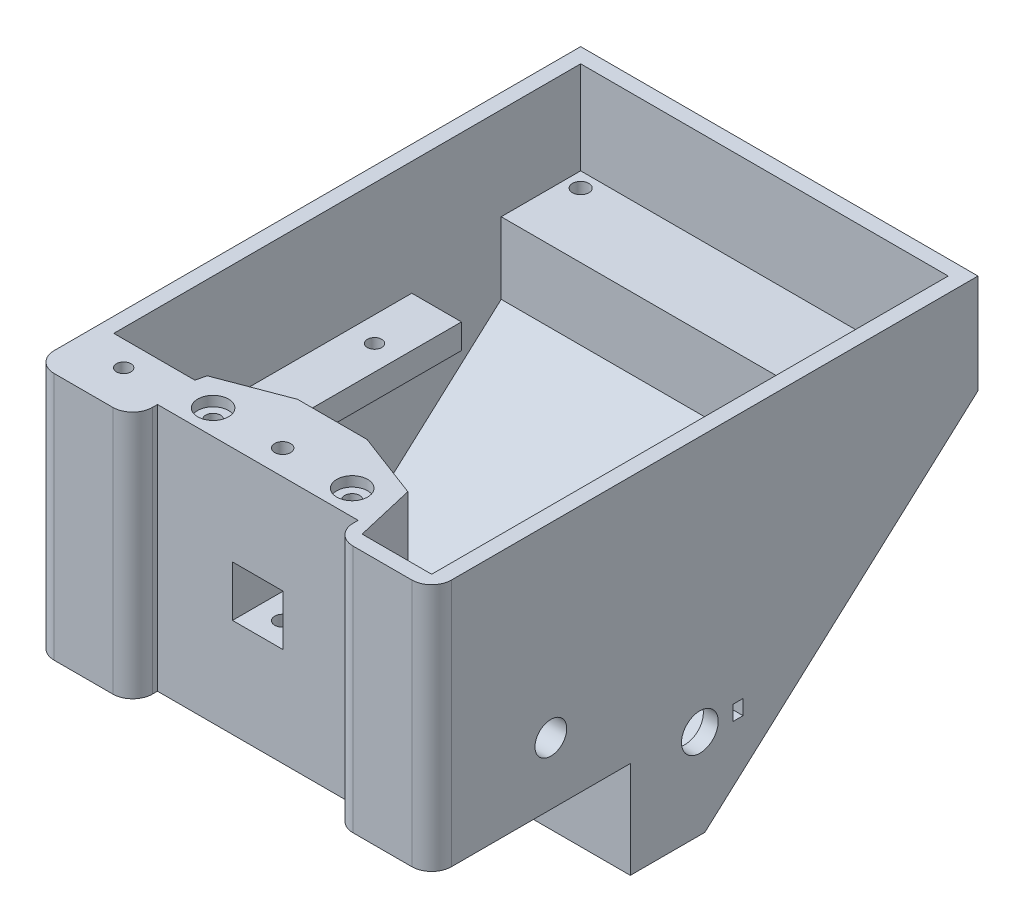
SolidWorks part; units mm, degrees
ref_plane "Спереди" through (0, 0, 0) normal (0, 0, 1) x (1, 0, 0)
ref_plane "Сверху" through (0, 0, 0) normal (0, 1, 0) x (1, 0, 0)
ref_plane "Справа" through (0, 0, 0) normal (1, 0, 0) x (0, 0, -1)
sketch "Sketch2" plane through (0, 0, 0) normal (1, 0, 0) x (0, 0, -1)
  line L0 (-27.3205, 20.9982) -> (-27.3205, -29.0018)
  line L1 (-27.3205, -29.0018) -> (12.6795, -29.0018)
  line L2 (12.6795, -29.0018) -> (12.6795, -48.5114)
  line L3 (12.6795, -48.5114) -> (27.6795, -48.5114)
  line L4 (82.6795, 20.9982) -> (82.6795, 0.9982)
  line L5 (82.6795, 20.9982) -> (-27.3205, 20.9982)
  line L6 (82.6795, 0.9982) -> (27.6795, -48.5114)
  dimension "D1" = 110
  dimension "D2" = 50
  dimension "D3" = 40
  dimension "D4" = 15
  dimension "D5" = 20
extrude "Boss-Extrude1" add sketch "Sketch2" along normal blind 80
shell "Shell1" thickness 3
sketch "Sketch3" plane through (0, 0, 24.3205) normal (0, 0, -1) x (-1, 0, 0)
  line L0 (-40, 20.9982) -> (-40, -26.0018) construction
  line L3 (-77, 20.9982) -> (-3, 20.9982) construction
  line L4 (-77, -26.0018) -> (-3, -26.0018) construction
  line L6 (-17, 20.9982) -> (-63, 20.9982)
  line L7 (-17, 20.9982) -> (-17, -26.0018)
  line L8 (-17, -26.0018) -> (-63, -26.0018)
  line L9 (-63, 20.9982) -> (-63, -26.0018)
  line L10 (-17, 20.9982) -> (-63, -26.0018) construction
  line L11 (-17, -26.0018) -> (-63, 20.9982) construction
  point P6 (-40, -2.5018)
  dimension "D1" = 46
extrude "Boss-Extrude2" add sketch "Sketch3" along normal blind 17
sketch "Sketch4" plane through (0, 0, 27.3205) normal (0, 0, 1) x (1, 0, 0)
  line L0 (0, 20.9982) -> (80, -29.0018) construction
  line L2 (45.1, -9.1018) -> (34.9, -9.1018)
  line L3 (45.1, -9.1018) -> (45.1, 1.0982)
  line L4 (45.1, 1.0982) -> (34.9, 1.0982)
  line L5 (34.9, -9.1018) -> (34.9, 1.0982)
  line L6 (45.1, -9.1018) -> (34.9, 1.0982) construction
  line L7 (45.1, 1.0982) -> (34.9, -9.1018) construction
  point P4 (40, -4.0018)
  dimension "D1" = 10.2
extrude "Cut-Extrude1" cut sketch "Sketch4" against normal up to surface (20 mm away) up to face at (40, -2.5018, 7.3205)
sketch "Sketch6" plane through (0, -29.0018, 0) normal (0, -1, 0) x (1, 0, 0)
  line L0 (40, 27.3205) -> (40, -12.6795) construction
  line L1 (47.5, -5.4795) -> (32.5, -5.4795) construction
  line L2 (47.5, -5.4795) -> (47.5, 7.3205) construction
  line L3 (47.5, 7.3205) -> (32.5, 7.3205) construction
  line L4 (32.5, -5.4795) -> (32.5, 7.3205) construction
  line L5 (47.5, -5.4795) -> (32.5, 7.3205) construction
  line L6 (47.5, 7.3205) -> (32.5, -5.4795) construction
  line L7 (80, -12.6795) -> (0, -12.6795) construction
  line L8 (51.5, 0.9205) -> (28.5, 0.9205) construction
  line L9 (80, 27.3205) -> (0, 27.3205) construction
  line L11 (44, 7.3205) -> (59, 7.3205)
  line L12 (44, 7.3205) -> (44, -5.4795)
  line L13 (44, -5.4795) -> (59, -5.4795)
  line L14 (59, 7.3205) -> (59, -5.4795)
  line L15 (44, 7.3205) -> (59, -5.4795) construction
  line L16 (44, -5.4795) -> (59, 7.3205) construction
  line L17 (36, 7.3205) -> (21, 7.3205)
  line L18 (36, 7.3205) -> (36, -5.4795)
  line L19 (36, -5.4795) -> (21, -5.4795)
  line L20 (21, 7.3205) -> (21, -5.4795)
  line L21 (36, 7.3205) -> (21, -5.4795) construction
  line L22 (36, -5.4795) -> (21, 7.3205) construction
  point P0 (40, 0.9205)
  point P14 (40, 0.9205)
  dimension "D1" = 15
  dimension "D2" = 12.8
  dimension "D3" = 8
  dimension "D4" = 20
extrude "Cut-Extrude2" cut sketch "Sketch6" against normal up to surface (3 mm away) up to face at (40, -26.0018, 10.0705)
sketch "Sketch7" plane through (0, 0, 27.3205) normal (0, 0, 1) x (1, 0, 0)
  line L0 (40, 20.9982) -> (40, -29.0018) construction
  line L1 (80, 20.9982) -> (0, 20.9982) construction
  line L2 (80, -29.0018) -> (0, -29.0018) construction
  line L4 (60.2, -29.0018) -> (19.8, -29.0018)
  line L5 (60.2, -29.0018) -> (60.2, 20.9982)
  line L6 (60.2, 20.9982) -> (19.8, 20.9982)
  line L7 (19.8, -29.0018) -> (19.8, 20.9982)
  line L8 (60.2, -29.0018) -> (19.8, 20.9982) construction
  line L9 (60.2, 20.9982) -> (19.8, -29.0018) construction
  point P6 (40, -4.0018)
  dimension "D1" = 40.4
extrude "Cut-Extrude3" cut sketch "Sketch7" against normal blind 5
fillet "Fillet1" radius 4 4 edges at (19.8, -4.0018, 27.3205) (60.2, -4.0018, 27.3205) (80, -4.0018, 27.3205) (0, -4.0018, 27.3205)
sketch "Sketch12" plane through (0, 20.9982, 0) normal (0, 1, 0) x (1, 0, 0)
  line L0 (19.8, -22.3205) -> (19.8, -12.3205) construction
  line L1 (19.8, -12.3205) -> (60.2, -12.3205) construction
  line L2 (60.2, -12.3205) -> (60.2, -22.3205) construction
  line L3 (33, -7.3205) -> (19.8, -12.3205)
  line L4 (17, -7.3205) -> (63, -7.3205) construction
  line L5 (19.8, -12.3205) -> (17, -24.3205)
  line L6 (17, -24.3205) -> (17, -7.3205)
  line L7 (17, -7.3205) -> (33, -7.3205)
  line L8 (47, -7.3205) -> (63, -7.3205)
  line L9 (63, -7.3205) -> (63, -24.3205)
  line L10 (63, -24.3205) -> (60.2, -12.3205)
  line L11 (60.2, -12.3205) -> (47, -7.3205)
  dimension "D1" = 10
  dimension "D2" = 16
extrude "Cut-Extrude7" cut sketch "Sketch12" against normal up to surface (47 mm away) up to face at (40, -26.0018, 5.4955)
sketch "Sketch13" plane through (0, 20.9982, 0) normal (0, 1, 0) x (1, 0, 0)
  line L0 (19.8, -22.3205) -> (19.8, -12.3205) construction
  line L1 (19.8, -12.3205) -> (60.2, -12.3205) construction
  line L2 (60.2, -12.3205) -> (60.2, -22.3205) construction
  line L3 (60.2, -17.3205) -> (19.8, -17.3205) construction
  circle A0 centre (26, -17.3205) radius 1.5
  circle A1 centre (54, -17.3205) radius 1.5
  point P14 (40, -17.3205)
  dimension "D1" = 3
  dimension "D2" = 28
  dimension "D3" = 14
  dimension "D4" = 6.2
extrude "Cut-Extrude8" cut sketch "Sketch13" against normal blind 25
sketch "Sketch14" plane through (0, 20.9982, 0) normal (0, 1, 0) x (1, 0, 0)
  circle A0 centre (26, -17.3205) radius 3.1
  circle A1 centre (54, -17.3205) radius 3.1
  dimension "D1" = 6.2
extrude "Cut-Extrude9" cut sketch "Sketch14" against normal blind 2
sketch "Sketch17" plane through (77, 0, 0) normal (-1, 0, 0) x (0, 0, 1)
  line L0 (-45.6795, -2.0018) -> (-0.6795, -2.0018)
  line L1 (-0.6795, -2.0018) -> (-0.6795, -7.0018)
  line L2 (-0.6795, -7.0018) -> (-45.6795, -7.0018)
  line L3 (-45.6795, -7.0018) -> (-45.6795, -2.0018)
  line L4 (-79.6795, 20.9982) -> (24.3205, 20.9982) construction
  line L5 (-79.6795, 2.3342) -> (-79.6795, 20.9982) construction
  dimension "D1" = 45
  dimension "D2" = 5
  dimension "D3" = 23
  dimension "D4" = 34
extrude "Boss-Extrude5" add sketch "Sketch17" along normal up to surface (74 mm away) up to face at (3, -14.0994, -24.0865)
sketch "Sketch18" plane through (0, -2.0018, 0) normal (0, 1, 0) x (1, 0, 0)
  line L0 (40, 0.6795) -> (40, 45.6795) construction
  line L1 (3, 0.6795) -> (77, 0.6795) construction
  line L2 (3, 45.6795) -> (77, 45.6795) construction
  line L3 (77, 0.6795) -> (77, 45.6795) construction
  line L4 (13, 0.6795) -> (67, 0.6795)
  line L5 (13, 0.6795) -> (13, 45.6795)
  line L6 (13, 45.6795) -> (67, 45.6795)
  line L7 (67, 0.6795) -> (67, 45.6795)
  line L8 (13, 0.6795) -> (67, 45.6795) construction
  line L9 (13, 45.6795) -> (67, 0.6795) construction
  point P6 (40, 23.1795)
  dimension "D1" = 10
extrude "Cut-Extrude10" cut sketch "Sketch18" against normal up to next
sketch "Sketch19" plane through (0, -2.0018, 0) normal (0, 1, 0) x (1, 0, 0)
  line L0 (72, 45.6795) -> (72, 0.6795) construction
  line L1 (67, 45.6795) -> (77, 45.6795) construction
  line L2 (67, 0.6795) -> (77, 0.6795) construction
  line L3 (8, 45.6795) -> (8, 0.6795) construction
  line L4 (3, 45.6795) -> (13, 45.6795) construction
  line L5 (3, 0.6795) -> (13, 0.6795) construction
  circle A0 centre (72, 37.1795) radius 1.45
  circle A1 centre (72, 6.1795) radius 1.45
  circle A2 centre (8, 33.1795) radius 1.45
  circle A3 centre (8, 6.1795) radius 1.45
  point P20 (72, 23.1795)
  point P21 (8, 23.1795)
  dimension "D1" = 2.9
  dimension "D2" = 14
  dimension "D3" = 17
  dimension "D4" = 17
  dimension "D5" = 10
extrude "Cut-Extrude11" cut sketch "Sketch19" against normal up to next
sketch "Sketch21" plane through (0, -26.0018, 0) normal (0, 1, 0) x (1, 0, 0)
  line L0 (3, -24.3205) -> (3, -14.3205)
  line L1 (3, -24.3205) -> (3, 15.6795) construction
  line L2 (3, -14.3205) -> (19.3333, -14.3205)
  line L3 (19.8, -12.3205) -> (17, -24.3205) construction
  line L4 (19.3333, -14.3205) -> (17, -24.3205)
  line L6 (3, -24.3205) -> (17, -24.3205)
  dimension "D1" = 10
extrude "Boss-Extrude6" add sketch "Sketch21" along normal up to surface (47 mm away) up to face at (54, 20.9982, 20.4205)
sketch "Sketch22" plane through (0, 20.9982, 0) normal (0, 1, 0) x (1, 0, 0)
  line L0 (0, 82.6795) -> (0, -23.3205) construction
  line L1 (15.8, -27.3205) -> (4, -27.3205) construction
  circle A0 centre (10, -19.3205) radius 1.45
  dimension "D1" = 2.9
  dimension "D2" = 10
  dimension "D3" = 8
extrude "Cut-Extrude12" cut sketch "Sketch22" against normal through all
sketch "Sketch24" plane through (80, 0, 0) normal (1, 0, 0) x (0, 0, -1)
  line L0 (12.6795, -48.5114) -> (27.6795, -48.5114) construction
  line L1 (12.6795, -29.0018) -> (12.6795, -48.5114) construction
  line L2 (18.1795, -30.5114) -> (18.1795, -19.0114) construction
  line L3 (18.1795, -19.0114) -> (35.1795, -19.0114) construction
  line L4 (35.1795, -19.0114) -> (35.1795, -30.5114) construction
  line L5 (26.6795, -19.0114) -> (26.6795, -39.0114) construction
  line L6 (30.3795, -30.5114) -> (34.3795, -30.5114) construction
  line L8 (33.3795, -32.0114) -> (35.3795, -32.0114)
  line L9 (33.3795, -32.0114) -> (33.3795, -29.0114)
  line L10 (33.3795, -29.0114) -> (35.3795, -29.0114)
  line L11 (35.3795, -32.0114) -> (35.3795, -29.0114)
  line L12 (33.3795, -32.0114) -> (35.3795, -29.0114) construction
  line L13 (33.3795, -29.0114) -> (35.3795, -32.0114) construction
  circle A0 centre (26.6795, -30.5114) radius 3.7
  circle A1 centre (26.6795, -30.5114) radius 8.5 construction
  dimension "D1" = 7.4
  dimension "D2" = 17
  dimension "D3" = 18
  dimension "D4" = 14
  dimension "D5" = 20
  dimension "D6" = 4
  dimension "D7" = 2
  dimension "D8" = 3
extrude "Cut-Extrude13" cut sketch "Sketch24" against normal up to next
sketch "Sketch26" plane through (3, 0, 0) normal (1, 0, 0) x (0, 0, -1)
  line L0 (79.6795, 2.3342) -> (63.6795, 2.3342)
  line L1 (63.6795, 2.3342) -> (63.6795, -12.0686)
  line L2 (26.5281, -45.5114) -> (79.6795, 2.3342) construction
  line L3 (63.6795, -12.0686) -> (79.6795, 2.3342)
  dimension "D1" = 16
extrude "Boss-Extrude7" add sketch "Sketch26" along normal up to surface (74 mm away) up to face at (77, -30.5114, -34.3795)
sketch "Sketch27" plane through (0, 2.3342, 0) normal (0, 1, 0) x (1, 0, 0)
  line L0 (3, 76.6795) -> (77, 76.6795) construction
  line L1 (3, 79.6795) -> (3, 63.6795) construction
  line L2 (77, 79.6795) -> (77, 63.6795) construction
  line L3 (80, 82.6795) -> (0, 82.6795) construction
  circle A0 centre (6, 76.6795) radius 1.65
  circle A1 centre (74, 76.6795) radius 1.65
  point P10 (40, 76.6795)
  dimension "D1" = 3.3
  dimension "D2" = 68
  dimension "D3" = 34
  dimension "D4" = 6
extrude "Cut-Extrude14" cut sketch "Sketch27" against normal blind 10
sketch "Sketch28" plane through (0, 2.3342, 0) normal (0, 1, 0) x (1, 0, 0)
  line L1 (74, 79.9295) -> (71.1854, 78.3045)
  line L2 (71.1854, 78.3045) -> (71.1854, 75.0545)
  line L3 (71.1854, 75.0545) -> (74, 73.4295)
  line L4 (74, 73.4295) -> (76.8146, 75.0545)
  line L5 (76.8146, 75.0545) -> (76.8146, 78.3045)
  line L6 (76.8146, 78.3045) -> (74, 79.9295)
  line L7 (6, 73.4295) -> (8.8146, 75.0545)
  line L8 (8.8146, 75.0545) -> (8.8146, 78.3045)
  line L9 (8.8146, 78.3045) -> (6, 79.9295)
  line L10 (6, 79.9295) -> (3.1854, 78.3045)
  line L11 (3.1854, 78.3045) -> (3.1854, 75.0545)
  line L12 (3.1854, 75.0545) -> (6, 73.4295)
  circle A0 centre (74, 76.6795) radius 3.25 construction
  circle A1 centre (6, 76.6795) radius 3.25 construction
  dimension "D1" = 6.5
extrude "Cut-Extrude15" cut sketch "Sketch28" against normal blind 32 from offset 3 offset against normal yes
sketch "Sketch29" plane through (0, -29.0018, 0) normal (0, -1, 0) x (1, 0, 0)
  line L0 (0, 23.3205) -> (0, -12.6795) construction
  line L1 (7.1854, 17.6955) -> (10, 16.0705)
  line L2 (10, 16.0705) -> (12.8146, 17.6955)
  line L3 (12.8146, 17.6955) -> (12.8146, 20.9455)
  line L4 (12.8146, 20.9455) -> (10, 22.5705)
  line L5 (10, 22.5705) -> (7.1854, 20.9455)
  line L6 (7.1854, 20.9455) -> (7.1854, 17.6955)
  circle A0 centre (10, 19.3205) radius 3.25 construction
  dimension "D1" = 6.5
extrude "Cut-Extrude16" cut sketch "Sketch29" against normal blind 30
sketch "Sketch30" plane through (0, -26.0018, 0) normal (0, 1, 0) x (1, 0, 0)
  line L0 (77, -24.3205) -> (63, -24.3205)
  line L1 (63, -24.3205) -> (60.2, -12.3205)
  line L2 (63, -24.3205) -> (60.2, -12.3205) construction
  line L3 (60.2, -12.3205) -> (77, -12.3205)
  line L4 (77, -24.3205) -> (77, 15.6795) construction
  line L5 (77, -12.3205) -> (77, -24.3205)
  dimension "D1" = 12
extrude "Boss-Extrude8" add sketch "Sketch30" along normal blind 20
sketch "Sketch31" plane through (0, -6.0018, 0) normal (0, 1, 0) x (1, 0, 0)
  line L0 (76, -27.3205) -> (64.2, -27.3205) construction
  line L1 (80, -23.3205) -> (80, 12.6795) construction
  circle A0 centre (72, -21.3205) radius 1.5
  dimension "D3" = 3
  dimension "D1" = 6
  dimension "D2" = 8
extrude "Cut-Extrude17" cut sketch "Sketch31" against normal through all
sketch "Sketch32" plane through (0, -29.0018, 0) normal (0, -1, 0) x (1, 0, 0)
  line L1 (72, 24.5705) -> (69.1854, 22.9455)
  line L2 (69.1854, 22.9455) -> (69.1854, 19.6955)
  line L3 (69.1854, 19.6955) -> (72, 18.0705)
  line L4 (72, 18.0705) -> (74.8146, 19.6955)
  line L5 (74.8146, 19.6955) -> (74.8146, 22.9455)
  line L6 (74.8146, 22.9455) -> (72, 24.5705)
  circle A0 centre (72, 21.3205) radius 3.25 construction
  dimension "D1" = 6.5
extrude "Cut-Extrude18" cut sketch "Sketch32" against normal blind 15
sketch "Sketch33" plane through (0, -2.0018, 0) normal (0, 1, 0) x (1, 0, 0)
  line L0 (67, 40.6795) -> (77, 40.6795)
  line L1 (67, 0.6795) -> (67, 45.6795) construction
  line L2 (77, 0.6795) -> (77, 45.6795) construction
  line L3 (77, 40.6795) -> (77, 45.6795)
  line L4 (77, 45.6795) -> (67, 45.6795)
  line L5 (67, 45.6795) -> (67, 40.6795)
  dimension "D1" = 5
extrude "Cut-Extrude19" cut sketch "Sketch33" against normal up to next
sketch "Sketch34" plane through (0, 20.9982, 0) normal (0, 1, 0) x (1, 0, 0)
  line L0 (54, -17.3205) -> (26, -17.3205) construction
  circle A0 centre (40, -17.3205) radius 1.6
  dimension "D1" = 3.2
extrude "Cut-Extrude20" cut sketch "Sketch34" against normal through all
sketch "Sketch36" plane through (0, -29.0018, 0) normal (0, -1, 0) x (1, 0, 0)
  line L1 (38.375, 20.1351) -> (36.75, 17.3205)
  line L2 (36.75, 17.3205) -> (38.375, 14.5059)
  line L3 (38.375, 14.5059) -> (41.625, 14.5059)
  line L4 (41.625, 14.5059) -> (43.25, 17.3205)
  line L5 (43.25, 17.3205) -> (41.625, 20.1351)
  line L6 (41.625, 20.1351) -> (38.375, 20.1351)
  circle A0 centre (40, 17.3205) radius 3.25 construction
  dimension "D1" = 6.5
extrude "Cut-Extrude22" cut sketch "Sketch36" against normal blind 14
sketch "Sketch37" plane through (80, 0, 0) normal (1, 0, 0) x (0, 0, -1)
  line L0 (-23.3205, -16.5114) -> (63.2281, -16.5114) construction
  line L1 (-23.3205, 20.9982) -> (-23.3205, -29.0018) construction
  line L2 (27.6795, -48.5114) -> (82.6795, 0.9982) construction
  line L3 (30.3795, -30.5114) -> (22.9795, -30.5114) construction
  circle A0 centre (-3.3205, -16.5114) radius 3.2
  circle A1 centre (26.6795, -30.5114) radius 3.7 construction
  point P14 (26.6795, -30.5114)
  dimension "D1" = 6.4
  dimension "D2" = 14
  dimension "D3" = 20
extrude "Cut-Extrude23" cut sketch "Sketch37" against normal up to next
sketch "Sketch38" plane through (77, 0, 0) normal (-1, 0, 0) x (0, 0, 1)
  line L0 (12.3205, -26.0018) -> (-15.6795, -26.0018) construction
  line L1 (8.3205, -7.021) -> (-1.6795, -7.021)
  line L2 (8.3205, -7.021) -> (8.3205, -26.0018)
  line L3 (8.3205, -26.0018) -> (-1.6795, -26.0018)
  line L4 (-1.6795, -7.021) -> (-1.6795, -26.0018)
  line L5 (8.3205, -7.021) -> (-1.6795, -26.0018) construction
  line L6 (8.3205, -26.0018) -> (-1.6795, -7.021) construction
  circle A0 centre (3.3205, -16.5114) radius 3.2
  point P0 (3.3205, -16.5114)
  dimension "D1" = 10
extrude "Boss-Extrude9" add sketch "Sketch38" along normal blind 3
